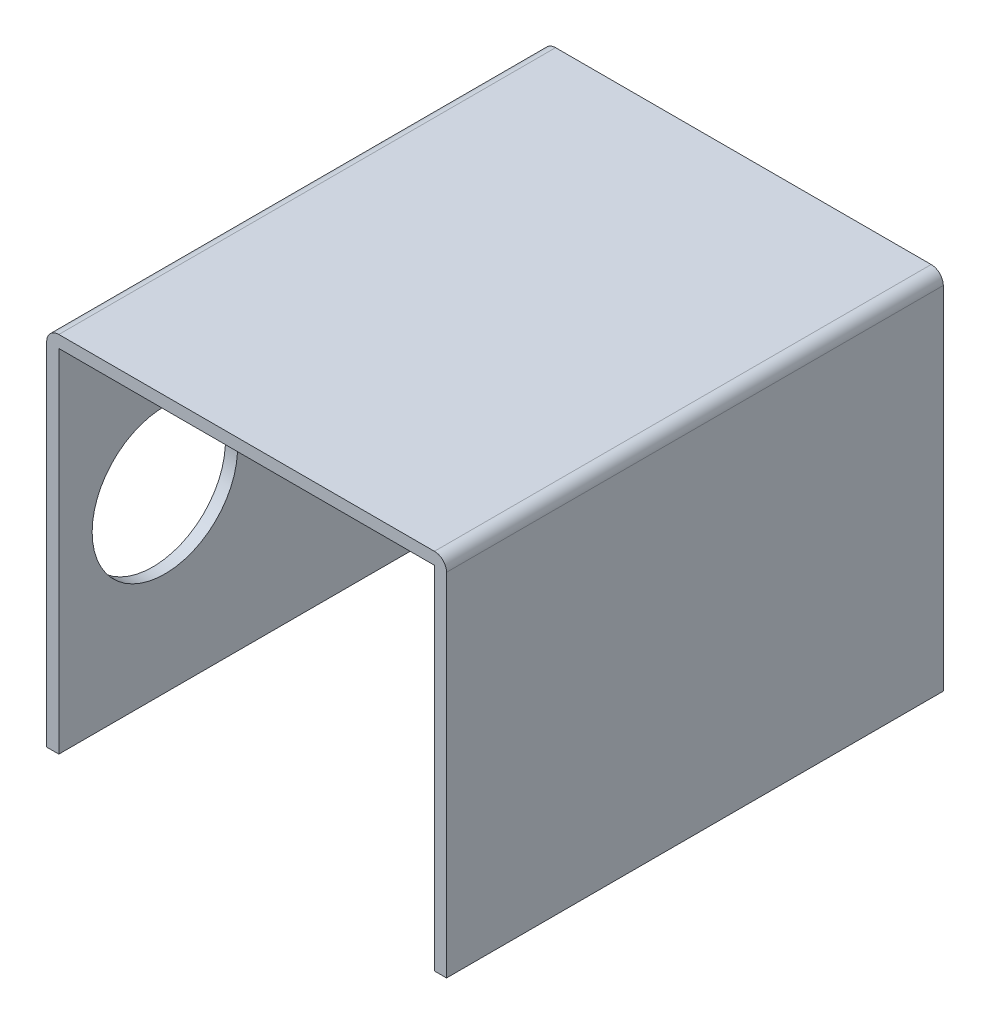
SolidWorks part; units mm, degrees
material "3003 Alaşım"
ref_plane "Ön Düzlem" through (0, 0, 0) normal (0, 0, 1) x (1, 0, 0)
ref_plane "Üst Düzlem" through (0, 0, 0) normal (0, 1, 0) x (1, 0, 0)
ref_plane "Sağ Düzlem" through (0, 0, 0) normal (1, 0, 0) x (0, 0, -1)
sketch "Çizim1" plane through (0, 0, 0) normal (0, 0, 1) x (1, 0, 0)
  line L0 (0, 0) -> (0, 29)
  line L1 (1, 30) -> (32, 30)
  line L2 (33, 29) -> (33, 0)
  arc A0 (0, 29) -> (1, 30) centre (1, 29) cw
  arc A1 (32, 30) -> (33, 29) centre (32, 29) cw
  point P7 (0, 30)
  point P10 (33, 30)
  dimension "D3" = 1
  dimension "D1" = 33
  dimension "D2" = 30
extrude "Ekstrüzyon-İnce1" add sketch "Çizim1" along normal blind 41 thin
sketch "Çizim2" plane through (0, 0, 0) normal (1, 0, 0) x (0, 0, -1)
  line L0 (-41, 14.5) -> (0, 14.5) construction
  line L1 (-41, 29) -> (-41, 0) construction
  line L2 (0, 29) -> (0, 0) construction
  line L3 (-20.5, 25.8154) -> (-20.5, 3.1846) construction
  line L4 (-32.25, 25.8154) -> (-32.25, 3.1846) construction
  line L5 (-8.75, 25.8154) -> (-8.75, 3.1846) construction
  circle A0 centre (-32.25, 14.5) radius 3
  circle A1 centre (-8.75, 14.5) radius 3
  point P9 (-20.5, 14.5)
  point P17 (0, 0)
  point P18 (0, 0)
  dimension "D1" = 11.75
  dimension "D2" = 11.75
extrude "Kes-Ekstrüzyon1" cut sketch "Çizim2" along normal blind 5
sketch "Çizim4" plane through (0, 0, 0) normal (-1, 0, 0) x (0, 0, 1)
  circle A0 centre (32.25, 14.5) radius 6
extrude "Kes-Ekstrüzyon3" cut sketch "Çizim4" against normal blind 22
